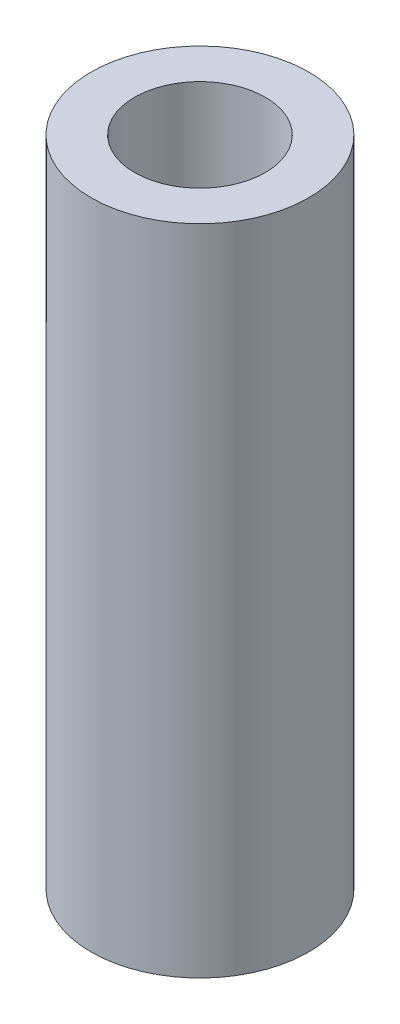
SolidWorks part; units mm, degrees
ref_plane "Front Plane" through (0, 0, 0) normal (0, 0, 1) x (1, 0, 0)
ref_plane "Top Plane" through (0, 0, 0) normal (0, 1, 0) x (1, 0, 0)
ref_plane "Right Plane" through (0, 0, 0) normal (1, 0, 0) x (0, 0, -1)
sketch "Sketch1" plane through (0, 0, 0) normal (0, 1, 0) x (1, 0, 0)
  circle A0 centre (0, 0) radius 2.5
  circle A1 centre (0, 0) radius 1.5
  dimension "D1" = 3
  dimension "D2" = 5
extrude "Boss-Extrude1" add sketch "Sketch1" along normal blind 15
